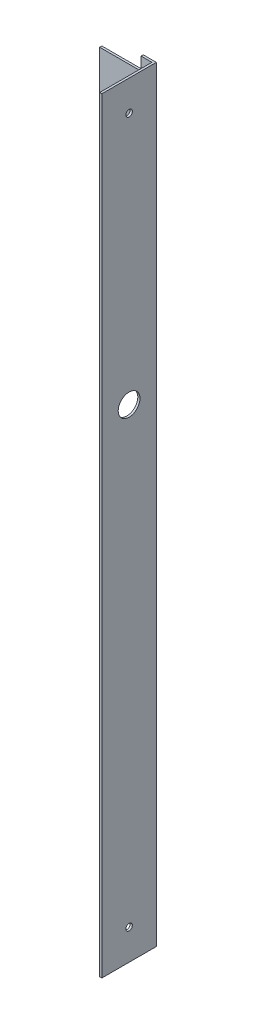
SolidWorks part; units mm, degrees
material "Aleación 1060"
ref_plane "Alzado" through (0, 0, 0) normal (0, 0, 1) x (1, 0, 0)
ref_plane "Planta" through (0, 0, 0) normal (0, 1, 0) x (1, 0, 0)
ref_plane "Vista lateral" through (0, 0, 0) normal (1, 0, 0) x (0, 0, -1)
sketch "Croquis1" plane through (0, 0, 0) normal (0, 0, 1) x (1, 0, 0)
  line L1 (-56.34, 62.1804) -> (-61.34, 62.1804)
  line L2 (-56.34, -289.8196) -> (-56.34, 62.1804)
  line L5 (-61.34, 62.1804) -> (-61.34, 56.1804)
  line L9 (-61.34, 56.1804) -> (-80.34, 56.1804)
  line L10 (-80.34, 56.1804) -> (-80.34, -13.8196)
  line L11 (-80.34, -13.8196) -> (-61.34, -13.8196)
  line L12 (-61.34, -13.8196) -> (-61.34, -213.8196)
  line L13 (-61.34, -213.8196) -> (-80.34, -213.8196)
  line L14 (-80.34, -213.8196) -> (-80.34, -283.8196)
  line L15 (-80.34, -283.8196) -> (-61.34, -283.8196)
  line L16 (-61.34, -283.8196) -> (-61.34, -289.8196)
  line L17 (-61.34, -289.8196) -> (-56.34, -289.8196)
  dimension "D1" = 352
  dimension "D4" = 200
  dimension "D2" = 6
  dimension "D3" = 6
sketch "Croquis2" plane through (0, 0, 0) normal (0, 0, 1) x (1, 0, 0)
  line L1 (-56.34, 62.1804) -> (-55.34, 62.1804)
  line L2 (-56.34, 62.1804) -> (-56.34, -289.8196)
  line L3 (-56.34, -289.8196) -> (-55.34, -289.8196)
  line L4 (-55.34, 62.1804) -> (-55.34, -289.8196)
  dimension "D1" = 1
  dimension "D2" = 352
extrude "Saliente-Extruir2" add sketch "Croquis2" along normal blind 25
sketch "Croquis5" plane through (-55.34, 0, 0) normal (1, 0, 0) x (0, 0, -1)
  line L0 (-25, 62.1804) -> (0, 62.1804) construction
  line L1 (-25, -289.8196) -> (0, -289.8196) construction
  line L2 (-25, -289.8196) -> (-25, 62.1804) construction
  line L3 (-25, 62.1804) -> (0, 62.1804) construction
  circle A0 centre (-12.5, 48.1804) radius 1.5
  circle A1 centre (-12.5, -275.8196) radius 1.5
  circle A2 centre (-12.5, -67.8196) radius 5
  dimension "D1" = 14
  dimension "D4" = 12.5
  dimension "D5" = 12.5
  dimension "D2" = 14
  dimension "D3" = 12.5
  dimension "D6" = 130
extrude "Cortar-Extruir2" cut sketch "Croquis5" against normal blind 1
extrude "Saliente-Extruir3" add sketch "Croquis1" along normal blind 1
